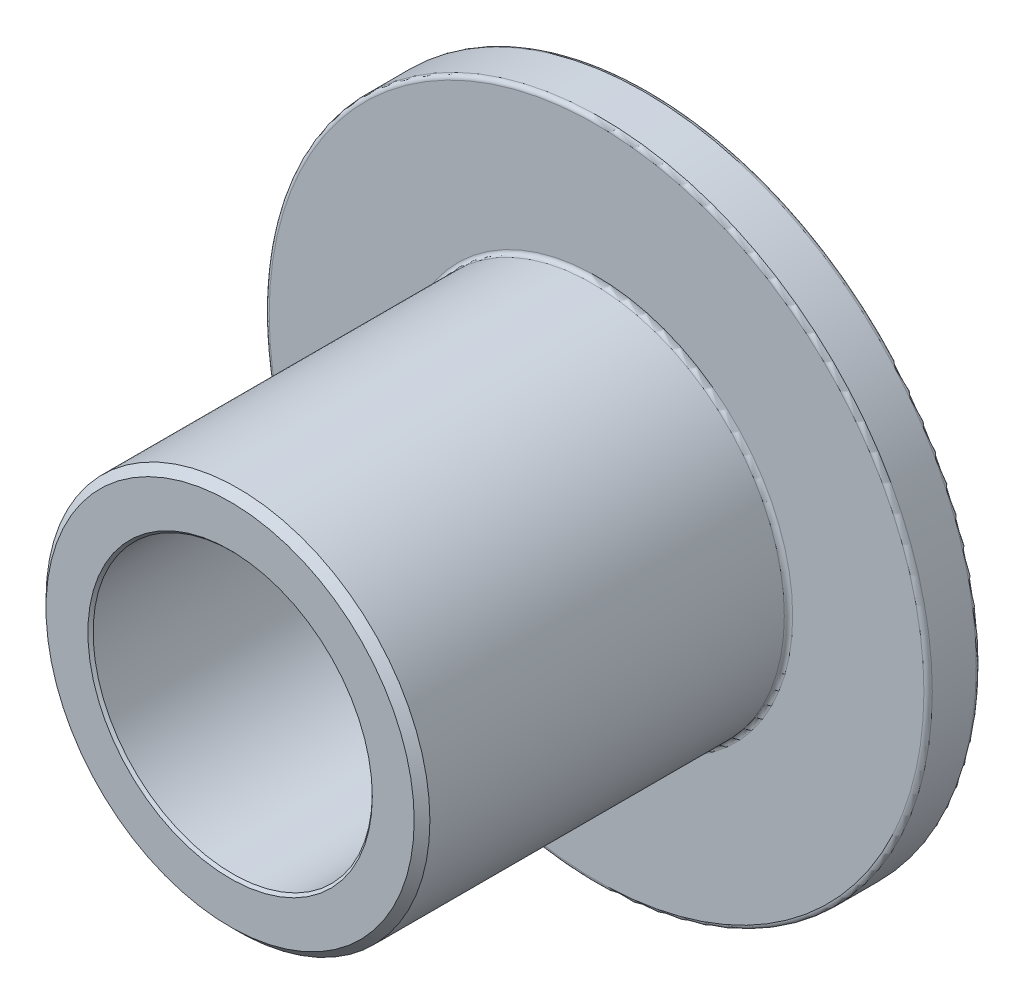
SolidWorks part; units mm, degrees
ref_plane "Front Plane" through (0, 0, 0) normal (0, 0, 1) x (1, 0, 0)
ref_plane "Top Plane" through (0, 0, 0) normal (0, 1, 0) x (1, 0, 0)
ref_plane "Right Plane" through (0, 0, 0) normal (1, 0, 0) x (0, 0, -1)
sketch "Sketch1" plane through (0, 0, 0) normal (0, 0, 1) x (1, 0, 0)
  circle A0 centre (0, 0) radius 2 construction
  circle A1 centre (0, 0) radius 2.75 construction
  circle A2 centre (0, 0) radius 4.75 construction
  point P5 (0, 4.75)
  dimension "ID" = 4
  dimension "OD" = 5.5
  dimension "Flange OD" = 9.5
sketch "Sketch2" plane through (0, 0, 0) normal (1, 0, 0) x (0, 0, -1)
  line L0 (-3, 0) -> (3, 0) construction
  line L1 (-3, 2.75) -> (-3, -2.75) construction
  line L2 (0, 2.75) -> (0, -2.75) construction
  line L3 (3, 4.75) -> (3, -4.75) construction
  line L4 (0, 4.75) -> (0, -4.75) construction
  line L5 (3, -4.75) -> (2.25, -4.75) construction
  dimension "Length" = 6
  dimension "Flange Thickness" = 0.75
sketch "Sketch3" plane through (0, 0, 0) normal (1, 0, 0) x (0, 0, -1)
  line L0 (3, -4.75) -> (2.25, -4.75)
  line L1 (2.25, -4.75) -> (2.25, -2.75)
  line L2 (2.25, -2.75) -> (-3, -2.75)
  line L3 (-3, -2.75) -> (-3, -2)
  line L4 (-3, 2.75) -> (-3, -2.75) construction
  line L5 (-3, -2) -> (3, -2)
  line L6 (3, 4.75) -> (3, -4.75) construction
  line L7 (3, -2) -> (3, -4.75)
  line L9 (0, 2) -> (0, -2) construction
  point P15 (0, -2)
revolve "Revolve1" add sketch "Sketch3" angle 360 about L0
chamfer "Chamfer1" distance 0.1125 angle 45 1 edges at (2.75, 0, 3)
chamfer "Chamfer2" distance 0.0375 angle 45 2 edges at (2, 0, -3) (2, 0, 3)
fillet "Fillet1" radius 0.06 3 edges at (4.75, 0, -3) (2.75, 0, -2.25) (4.75, 0, -2.25)
equation "\"D1@Chamfer1\"=(\"OD@Sketch1\"-\"ID@Sketch1\")*0.075"
equation "\"D1@Chamfer2\"=(\"OD@Sketch1\"-\"ID@Sketch1\")*0.025"
equation "\"D1@Fillet1\"=(\"Flange OD@Sketch1\"-\"OD@Sketch1\")*0.015"
